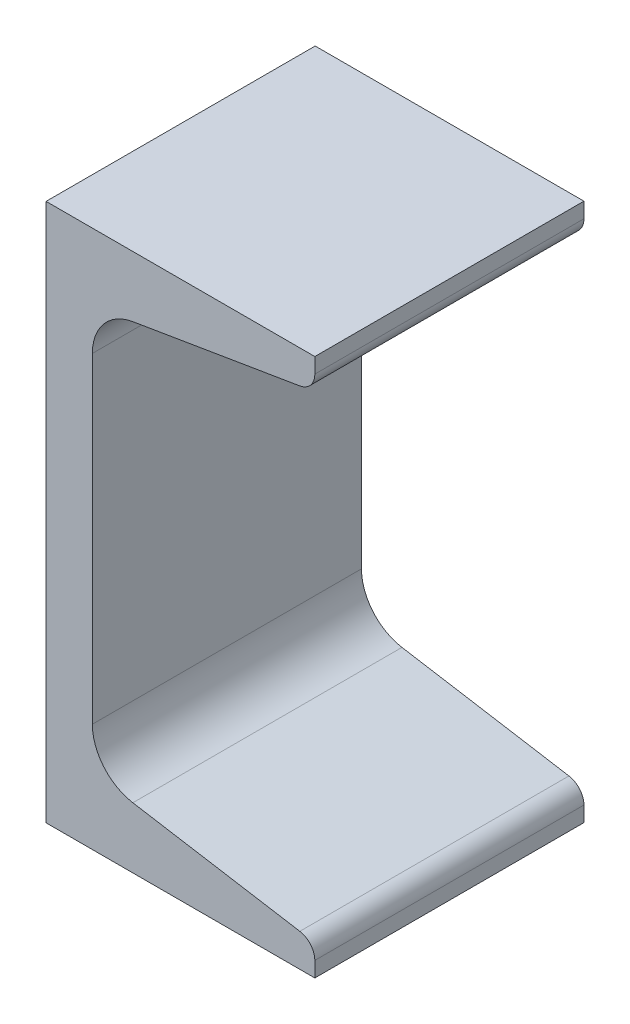
SolidWorks part; units mm, degrees
ref_plane "Front" through (0, 0, 0) normal (0, 0, 1) x (1, 0, 0)
ref_plane "Top" through (0, 0, 0) normal (0, 1, 0) x (1, 0, 0)
ref_plane "Right" through (0, 0, 0) normal (1, 0, 0) x (0, 0, -1)
sketch "Sketch1" plane through (0, 0, 0) normal (0, 0, 1) x (1, 0, 0)
  line L0 (0, 0) -> (0, 76.2)
  line L1 (0, 76.2) -> (38.0492, 76.2)
  line L2 (0, 0) -> (38.0492, 0)
  line L5 (31.75, 6.9342) -> (6.35, 6.9342) construction
  line L12 (6.5532, 60.8314) -> (6.5532, 15.3686)
  line L15 (38.0492, 76.2) -> (38.0492, 74.0423)
  line L16 (38.0492, 0) -> (38.0492, 2.1577)
  line L17 (12.2837, 67.5961) -> (35.9268, 71.5369)
  line L18 (12.2837, 8.6039) -> (35.9268, 4.6631)
  arc A9 (6.5532, 15.3686) -> (12.2837, 8.6039) centre (13.4112, 15.3686) ccw
  arc A10 (6.5532, 60.8314) -> (12.2837, 67.5961) centre (13.4112, 60.8314) cw
  arc A11 (38.0492, 74.0423) -> (35.9268, 71.5369) centre (35.5092, 74.0423) cw
  arc A12 (38.0492, 2.1577) -> (35.9268, 4.6631) centre (35.5092, 2.1577) ccw
  dimension "RI" = 6.858
  dimension "D2" = 9.463
  dimension "RA" = 2.54
  dimension "Depth" = 76.2
  dimension "BF" = 38.0492
  dimension "TW" = 6.5532
  dimension "flange" = 2.1577
  dimension "TF" = 6.9342
extrude "Boss-Extrude1" add sketch "Sketch1" along normal mid plane 38.1
